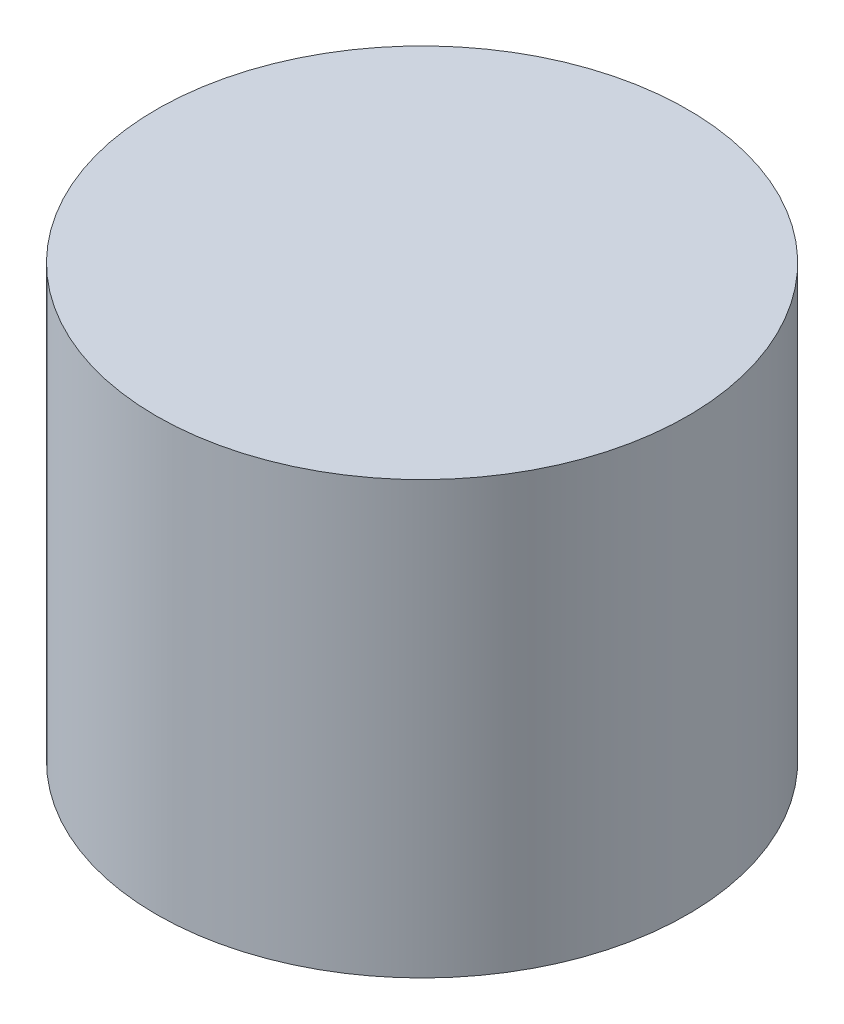
SolidWorks part; units mm, degrees
ref_plane "Front Plane" through (0, 0, 0) normal (0, 0, 1) x (1, 0, 0)
ref_plane "Top Plane" through (0, 0, 0) normal (0, 1, 0) x (1, 0, 0)
ref_plane "Right Plane" through (0, 0, 0) normal (1, 0, 0) x (0, 0, -1)
sketch "Sketch1" plane through (0, 0, 0) normal (0, 1, 0) x (1, 0, 0)
  circle A0 centre (0, 0) radius 50.8
extrude "Boss-Extrude1" add sketch "Sketch1" along normal blind 82.55
hole_wizard "1/4-20 Tapped Hole1" positions "Sketch3" profile "Sketch2" tap size "1/4-20" standard "ANSI Inch"
sketch "Sketch3" plane through (0, 0, 0) normal (0, -1, 0) x (-1, 0, 0)
  point P0 (0, 0)
sketch "Sketch2" plane through (0, 0, 0) normal (1, 0, 0) x (0, 0, -1)
  line L0 (0, 0) -> (0, 20.5838)
  line L1 (0, 20.5838) -> (2.5527, 19.05)
  line L2 (2.5527, 19.05) -> (2.5527, 0)
  line L5 (2.5527, 0) -> (0, 0)
  line L10 (0, 20.5838) -> (-2.5527, 19.05) construction
  line L11 (0, -6.35) -> (0, 107.95) construction
  dimension "Tap Drill Dia." = 5.1054
  dimension "Tap Drill Depth" = 19.05
  dimension "Drill Angle" = 118
cosmetic thread "Hole Thread1" parameters "D1"=12.7, "D2"=6.35
sketch "Sketch4" plane through (0, 0, 0) normal (0, -1, 0) x (-1, 0, 0)
  point P0 (0, 44.45)
  point P1 (0, -44.45)
  dimension "D1" = 44.45
  dimension "D2" = 44.45
hole_wizard "5/32 (0.15625) Diameter Hole1" positions "Sketch6" profile "Sketch5" hole size "5/32" standard "ANSI Inch"
sketch "Sketch6" plane through (0, 0, 0) normal (0, -1, 0) x (-1, 0, 0)
  point P0 (0, 44.45)
  point P3 (0, -44.45)
sketch "Sketch5" plane through (0, 0, -44.45) normal (1, 0, 0) x (0, 0, -1)
  line L0 (0, 0) -> (0, 6.2723)
  line L1 (0, 6.2723) -> (1.9844, 5.08)
  line L2 (1.9844, 5.08) -> (1.9844, 0)
  line L5 (1.9844, 0) -> (0, 0)
  line L10 (0, 6.2723) -> (-1.9844, 5.08) construction
  line L11 (0, -6.35) -> (0, 107.95) construction
  dimension "Hole Dia." = 3.9688
  dimension "Hole Depth" = 5.08
  dimension "Drill Angle" = 118
